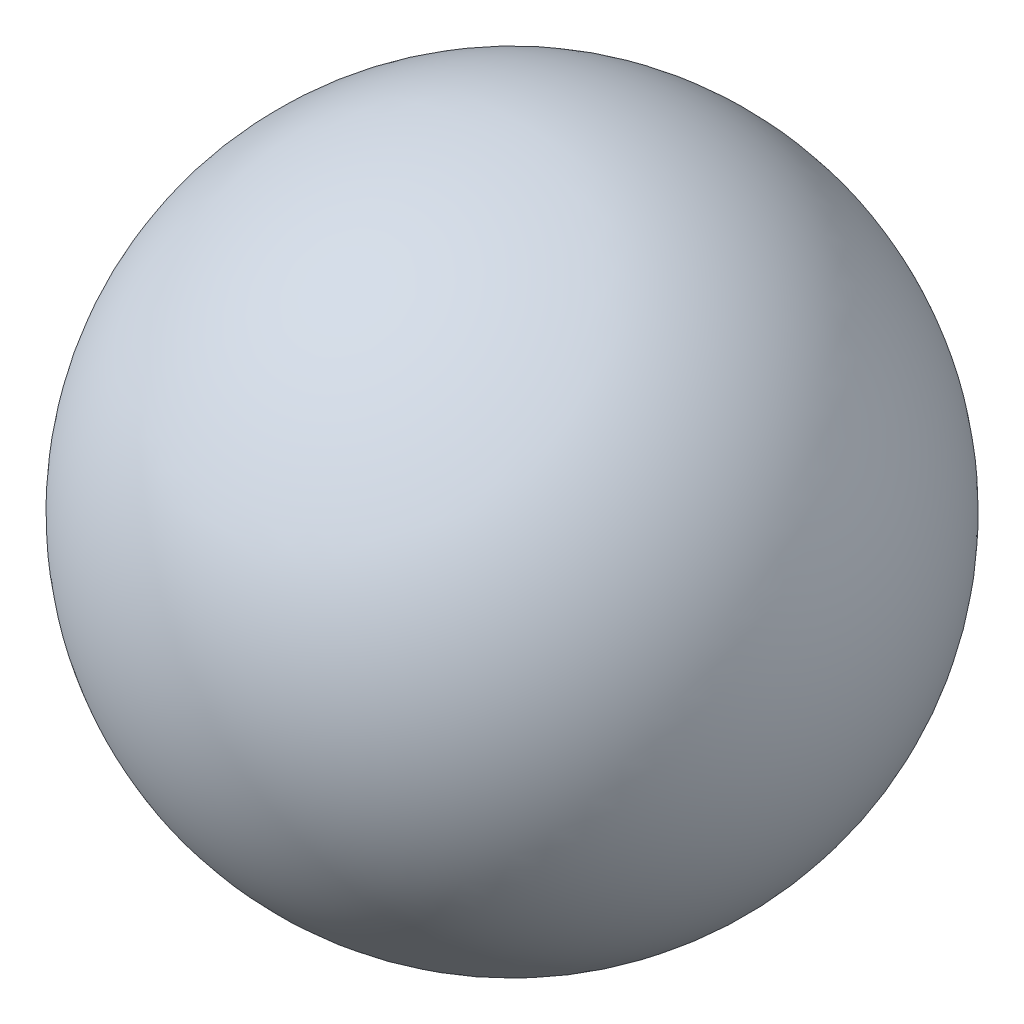
SolidWorks part; units mm, degrees
ref_plane "Front Plane" through (0, 0, 0) normal (0, 0, 1) x (1, 0, 0)
ref_plane "Top Plane" through (0, 0, 0) normal (0, 1, 0) x (1, 0, 0)
ref_plane "Right Plane" through (0, 0, 0) normal (1, 0, 0) x (0, 0, -1)
sketch "Sketch1" plane through (0, 0, 0) normal (0, 1, 0) x (1, 0, 0)
  line L0 (0, 0) -> (0, 1.9)
  arc A0 (0, 0) -> (0, 1.9) centre (0, 0.95) cw
  dimension "D1" = 1.9
revolve "Revolve1" add sketch "Sketch1" angle 360 about L0
